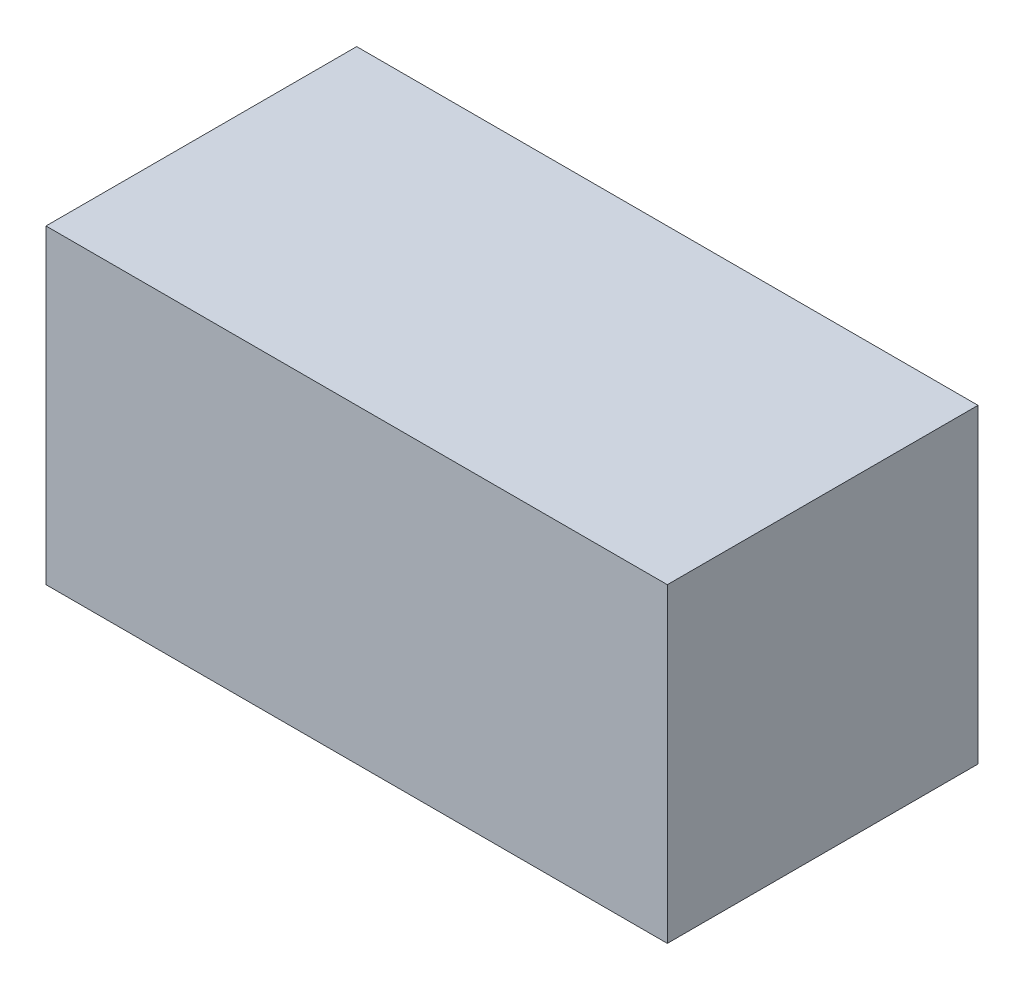
SolidWorks part; units mm, degrees
ref_plane "Front Plane" through (0, 0, 0) normal (0, 0, 1) x (1, 0, 0)
ref_plane "Top Plane" through (0, 0, 0) normal (0, 1, 0) x (1, 0, 0)
ref_plane "Right Plane" through (0, 0, 0) normal (1, 0, 0) x (0, 0, -1)
sketch "Sketch1" plane through (0, 0, 0) normal (0, 1, 0) x (1, 0, 0)
  line L1 (10, -5) -> (-10, -5)
  line L2 (10, -5) -> (10, 5)
  line L3 (10, 5) -> (-10, 5)
  line L4 (-10, -5) -> (-10, 5)
  line L5 (10, -5) -> (-10, 5) construction
  line L6 (10, 5) -> (-10, -5) construction
  point P0 (0, 0)
  dimension "D1" = 20
  dimension "D2" = 10
extrude "Boss-Extrude1" add sketch "Sketch1" along normal mid plane 10
equation "\"width\"=20"
equation "\"D1@Sketch1\"=\"width\""
equation "\"D2@Sketch1\"=\"width\"/2"
equation "\"D1@Boss-Extrude1\"=\"width\"/2"
